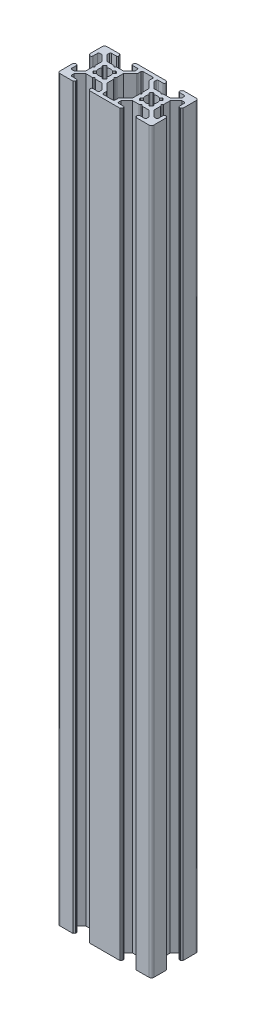
SolidWorks part; units mm, degrees
ref_plane "Front Plane" through (0, 0, 0) normal (0, 0, 1) x (1, 0, 0)
ref_plane "Top Plane" through (0, 0, 0) normal (0, 1, 0) x (1, 0, 0)
ref_plane "Right Plane" through (0, 0, 0) normal (1, 0, 0) x (0, 0, -1)
sketch "Sketch2" plane through (0, 0, 0) normal (0, 1, 0) x (1, 0, 0)
  line L0 (0, 13) -> (1.5, 13)
  line L1 (0, 0) -> (40, 0)
  line L2 (0, 0) -> (0, 20)
  line L3 (0, 20) -> (40, 20)
  line L4 (40, 0) -> (40, 20)
  line L9 (5.5, 6.5) -> (3, 4)
  line L10 (3, 4) -> (1.5, 4)
  line L11 (1.5, 4) -> (1.5, 7)
  line L12 (1.5, 7) -> (0, 7)
  line L13 (0, 7) -> (0, 13)
  line L14 (1.5, 13) -> (1.5, 16)
  line L15 (1.5, 16) -> (3, 16)
  line L16 (3, 16) -> (5.5, 13.5)
  line L17 (5.5, 10.5) -> (6, 10)
  line L18 (6, 10) -> (5.5, 9.5)
  line L19 (5.5, 9.5) -> (5.5, 10.5)
  line L20 (20, 20) -> (20, 0) construction
  line L31 (7, 18.5) -> (7, 20)
  line L32 (7, 18.5) -> (4, 18.5)
  line L33 (4, 18.5) -> (4, 17)
  line L34 (4, 17) -> (6.5, 14.5)
  line L38 (16, 18.5) -> (13, 18.5)
  line L39 (13, 18.5) -> (13, 20)
  line L40 (7, 20) -> (13, 20)
  line L41 (16, 18.5) -> (16, 17)
  line L42 (16, 17) -> (13.5, 14.5)
  line L53 (0, 10) -> (40, 10) construction
  line L89 (17.5, 18.5) -> (22.5, 18.5)
  line L90 (22.5, 18.5) -> (22.5, 16.5)
  line L91 (22.5, 16.5) -> (25.5, 13.5)
  line L92 (25.5, 13.5) -> (25.5, 6.5)
  line L93 (25.5, 6.5) -> (22.5, 3.5)
  line L94 (22.5, 3.5) -> (22.5, 1.5)
  line L95 (22.5, 1.5) -> (17.5, 1.5)
  line L96 (17.5, 1.5) -> (17.5, 3.5)
  line L97 (17.5, 3.5) -> (14.5, 6.5)
  line L98 (14.5, 6.5) -> (14.5, 13.5)
  line L99 (14.5, 13.5) -> (17.5, 16.5)
  line L100 (17.5, 16.5) -> (17.5, 18.5)
  line L102 (5.5, 13.5) -> (5.5, 10)
  line L103 (5.5, 10) -> (5.5, 6.5)
  line L104 (13.5, 14.5) -> (10, 14.5)
  line L105 (10, 14.5) -> (6.5, 14.5)
  line L106 (14.5, 10.5) -> (14.5, 9.5)
  line L107 (14.5, 9.5) -> (14, 10)
  line L108 (14, 10) -> (14.5, 10.5)
  line L109 (7, 18.5) -> (13, 18.5) construction
  line L110 (9.5, 14.5) -> (10.5, 14.5)
  line L111 (10.5, 14.5) -> (10, 14)
  line L112 (10, 14) -> (9.5, 14.5)
  line L113 (10.5, 5.5) -> (10, 6)
  line L114 (9.5, 5.5) -> (10.5, 5.5)
  line L115 (10, 6) -> (9.5, 5.5)
  line L116 (13.5, 5.5) -> (10, 5.5)
  line L117 (16, 3) -> (13.5, 5.5)
  line L118 (16, 1.5) -> (16, 3)
  line L119 (16, 1.5) -> (13, 1.5)
  line L120 (13, 1.5) -> (13, 0)
  line L121 (7, 0) -> (13, 0)
  line L122 (7, 1.5) -> (7, 0)
  line L123 (7, 1.5) -> (4, 1.5)
  line L124 (4, 1.5) -> (4, 3)
  line L125 (4, 3) -> (6.5, 5.5)
  line L126 (10, 5.5) -> (6.5, 5.5)
  line L127 (30.5, 5.5) -> (29.5, 5.5)
  line L128 (30, 6) -> (30.5, 5.5)
  line L129 (29.5, 5.5) -> (30, 6)
  line L130 (24, 3) -> (26.5, 5.5)
  line L131 (24, 1.5) -> (24, 3)
  line L132 (24, 1.5) -> (27, 1.5)
  line L133 (27, 1.5) -> (27, 0)
  line L134 (33, 0) -> (27, 0)
  line L135 (33, 1.5) -> (33, 0)
  line L136 (33, 1.5) -> (36, 1.5)
  line L137 (36, 1.5) -> (36, 3)
  line L138 (36, 3) -> (33.5, 5.5)
  line L139 (30, 5.5) -> (33.5, 5.5)
  line L140 (26.5, 5.5) -> (30, 5.5)
  line L141 (34, 10) -> (34.5, 9.5)
  line L142 (34.5, 10.5) -> (34, 10)
  line L143 (34.5, 9.5) -> (34.5, 10.5)
  line L144 (34.5, 13.5) -> (34.5, 10)
  line L145 (37, 16) -> (34.5, 13.5)
  line L146 (38.5, 16) -> (37, 16)
  line L147 (38.5, 13) -> (38.5, 16)
  line L148 (40, 13) -> (38.5, 13)
  line L149 (40, 7) -> (40, 13)
  line L150 (38.5, 7) -> (40, 7)
  line L151 (38.5, 4) -> (38.5, 7)
  line L152 (37, 4) -> (38.5, 4)
  line L153 (34.5, 6.5) -> (37, 4)
  line L154 (34.5, 10) -> (34.5, 6.5)
  line L155 (29.5, 14.5) -> (30, 14)
  line L156 (30.5, 14.5) -> (29.5, 14.5)
  line L157 (30, 14) -> (30.5, 14.5)
  line L158 (26.5, 14.5) -> (30, 14.5)
  line L159 (24, 17) -> (26.5, 14.5)
  line L160 (24, 18.5) -> (24, 17)
  line L161 (24, 18.5) -> (27, 18.5)
  line L162 (27, 18.5) -> (27, 20)
  line L163 (33, 20) -> (27, 20)
  line L164 (33, 18.5) -> (33, 20)
  line L165 (33, 18.5) -> (36, 18.5)
  line L166 (36, 18.5) -> (36, 17)
  line L167 (36, 17) -> (33.5, 14.5)
  line L168 (30, 14.5) -> (33.5, 14.5)
  line L169 (13.5, 14.5) -> (14.5, 13.5) construction
  line L170 (5.5, 6.5) -> (6.5, 5.5) construction
  line L171 (6.5, 14.5) -> (5.5, 13.5) construction
  line L172 (14.5, 6.5) -> (13.5, 5.5) construction
  line L173 (14.5, 10.5) -> (10.5, 14.5) construction
  line L174 (10.5, 5.5) -> (14.5, 9.5) construction
  line L175 (9.5, 5.5) -> (5.5, 9.5) construction
  line L176 (5.5, 10.5) -> (9.5, 14.5) construction
  line L177 (12, 13) -> (13, 12)
  line L178 (13, 12) -> (8, 7)
  line L179 (8, 7) -> (7, 8)
  line L180 (7, 8) -> (12, 13)
  line L181 (8, 13) -> (13, 8)
  line L182 (13, 8) -> (12, 7)
  line L183 (12, 7) -> (7, 12)
  line L184 (7, 12) -> (8, 13)
  line L185 (28, 7) -> (33, 12)
  line L186 (27, 8) -> (28, 7)
  line L187 (32, 13) -> (27, 8)
  line L188 (33, 12) -> (32, 13)
  line L189 (32, 7) -> (33, 8)
  line L190 (27, 12) -> (32, 7)
  line L191 (28, 13) -> (27, 12)
  line L192 (33, 8) -> (28, 13)
  line L193 (13.5, 20) -> (13, 20)
  line L194 (13, 19.5) -> (13, 20)
  line L195 (6.5, 20) -> (7, 20)
  line L196 (0, 13.5) -> (0, 13)
  line L197 (0.25, 7) -> (0, 7)
  line L198 (7, 19.5) -> (7, 20)
  line L199 (0.25, 7) -> (0, 7)
  line L200 (33, 19.5) -> (33, 20)
  line L201 (33.5, 20) -> (33, 20)
  line L202 (27, 19.5) -> (27, 20)
  line L203 (26.5, 20) -> (27, 20)
  line L204 (33, 0.5) -> (33, 0)
  line L205 (33.5, 0) -> (33, 0)
  line L206 (27, 0.5) -> (27, 0)
  line L207 (26.5, 0) -> (27, 0)
  line L208 (13, 0.5) -> (13, 0)
  line L209 (13.5, 0) -> (13, 0)
  line L210 (7, 0.5) -> (7, 0)
  line L211 (6.5, 0) -> (7, 0)
  line L212 (0.5, 13) -> (0, 13)
  line L213 (0, 6.75) -> (0, 7)
  line L214 (0, 6.75) -> (0, 7)
  line L215 (0, 7) -> (0.25, 7)
  line L216 (0, 6.5) -> (0, 7)
  line L217 (0, 7) -> (0.5, 7)
  line L218 (39.5, 13) -> (40, 13)
  line L219 (40, 13.5) -> (40, 13)
  line L220 (40, 6.5) -> (40, 7)
  line L221 (40, 7) -> (39.5, 7)
  line L222 (25.5, 9.5) -> (26, 10)
  line L223 (25.5, 10.5) -> (25.5, 9.5)
  line L224 (26, 10) -> (25.5, 10.5)
  circle A0 centre (10, 10) radius 2.5
  circle A1 centre (30, 10) radius 2.5
  arc A2 (13.5, 20) -> (13, 19.5) centre (13, 20) cw
  arc A3 (7, 19.5) -> (6.5, 20) centre (7, 20) cw
  arc A4 (0.5, 13) -> (0, 13.5) centre (0, 13) ccw
  arc A5 (0.5, 7) -> (0, 6.5) centre (0, 7) cw
  arc A6 (33, 19.5) -> (33.5, 20) centre (33, 20) ccw
  arc A7 (26.5, 20) -> (27, 19.5) centre (27, 20) ccw
  arc A8 (33, 0.5) -> (33.5, 0) centre (33, 0) cw
  arc A9 (26.5, 0) -> (27, 0.5) centre (27, 0) cw
  arc A10 (13.5, 0) -> (13, 0.5) centre (13, 0) ccw
  arc A11 (7, 0.5) -> (6.5, 0) centre (7, 0) ccw
  arc A12 (39.5, 13) -> (40, 13.5) centre (40, 13) cw
  arc A13 (39.5, 7) -> (40, 6.5) centre (40, 7) ccw
  point P19 (20, 10)
  point P103 (14.5, 10)
  dimension "D31" = 5
  dimension "D32" = 0.5
  dimension "D33" = 0.5
  dimension "D34" = 0.5
  dimension "D35" = 0.5
  dimension "D1" = 40
  dimension "D2" = 20
  dimension "D3" = 7
  dimension "D4" = 7
  dimension "D5" = 1.5
  dimension "D6" = 1.5
  dimension "D7" = 3.5
  dimension "D8" = 1.5
  dimension "D9" = 1.5
  dimension "D10" = 3
  dimension "D11" = 3
  dimension "D12" = 3.5
  dimension "D13" = 0.5
  dimension "D14" = 0.5
  dimension "D15" = 7
  dimension "D16" = 6
  dimension "D17" = 1.5
  dimension "D18" = 1.5
  dimension "D19" = 3
  dimension "D20" = 3
  dimension "D21" = 0.5
  dimension "D22" = 1.5
  dimension "D23" = 5.5
  dimension "D24" = 0.5
  dimension "D25" = 0.5
  dimension "D26" = 1.5
  dimension "D27" = 1.5
  dimension "D28" = 2
  dimension "D29" = 2
  dimension "D30" = 0.5
extrude "Boss-Extrude1" add sketch "Sketch2" along normal blind 315 contours L168 L157 L155 L158 L159 L160 L161 L162 L3 L39 L38 L41 L42 L104 L111 L112 L105 L34 L33 L32 L31 L2 L0 L14 L15 L16 L102 L17 L18 L103 L9 L10 L11 L12 L1 L122 L123 L124 L125 L126 L115 L113 L116 L117 L118 L119 L120 L133
fillet "Fillet1" radius 1 4 edges at (40, 157.5, -20) (40, 157.5, 0) (0, 157.5, 0) (0, 157.5, -20)
fillet "Fillet2" radius 0.5 6 edges at (13, 157.5, -18.5) (16, 157.5, -18.5) (10.5, 157.5, -14.5) (9.5, 157.5, -14.5) (4, 157.5, -18.5) (7, 157.5, -18.5)
fillet "Fillet3" radius 0.25 8 edges at (8, 157.5, -7) (7, 157.5, -8) (12, 157.5, -7) (13, 157.5, -8) (13, 157.5, -12) (12, 157.5, -13) (7, 157.5, -12) (8, 157.5, -13)
fillet "Fillet5" radius 0.25 8 edges at (27, 157.5, -8) (28, 157.5, -7) (32, 157.5, -7) (33, 157.5, -8) (33, 157.5, -12) (32, 157.5, -13) (27, 157.5, -12) (28, 157.5, -13)
fillet "Fillet6" radius 0.5 30 edges at (36, 157.5, -18.5) (33, 157.5, -18.5) (30.5, 157.5, -14.5) (29.5, 157.5, -14.5) (24, 157.5, -18.5) (27, 157.5, -18.5) (38.5, 157.5, -4) (38.5, 157.5, -7) (34.5, 157.5, -9.5) (34.5, 157.5, -10.5) (38.5, 157.5, -16) (38.5, 157.5, -13) (24, 157.5, -1.5) (27, 157.5, -1.5) (29.5, 157.5, -5.5) (30.5, 157.5, -5.5) (36, 157.5, -1.5) (33, 157.5, -1.5) (4, 157.5, -1.5) (7, 157.5, -1.5) (9.5, 157.5, -5.5) (10.5, 157.5, -5.5) (16, 157.5, -1.5) (13, 157.5, -1.5) (5.5, 157.5, -10.5) (5.5, 157.5, -9.5) (1.5, 157.5, -4) (1.5, 157.5, -7) (1.5, 157.5, -16) (1.5, 157.5, -13)
fillet "Fillet7" radius 0.5 8 edges at (22.5, 157.5, -3.5) (22.5, 157.5, -1.5) (17.5, 157.5, -3.5) (17.5, 157.5, -1.5) (17.5, 157.5, -16.5) (22.5, 157.5, -16.5) (22.5, 157.5, -18.5) (17.5, 157.5, -18.5)
fillet "Fillet8" radius 0.5 4 edges at (25.5, 157.5, -9.5) (25.5, 157.5, -10.5) (14.5, 157.5, -9.5) (14.5, 157.5, -10.5)
